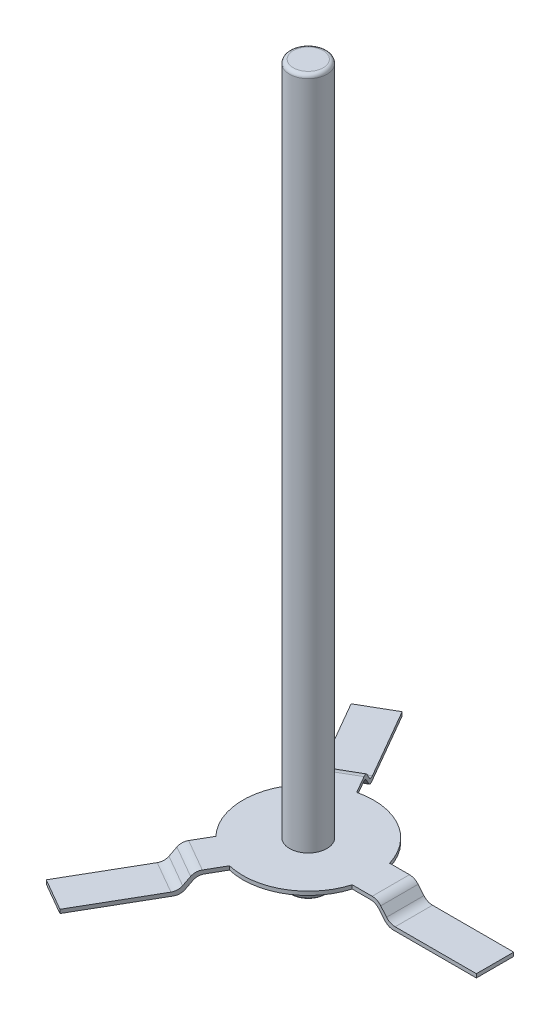
SolidWorks part; units mm, degrees
material "Ст. 3кп ГОСТ 380-2005"
ref_plane "Спереди" through (0, 0, 0) normal (0, 0, 1) x (1, 0, 0)
ref_plane "Сверху" through (0, 0, 0) normal (0, 1, 0) x (1, 0, 0)
ref_plane "Справа" through (0, 0, 0) normal (1, 0, 0) x (0, 0, -1)
sketch "Эскиз1" plane through (0, 0, 0) normal (0, 1, 0) x (1, 0, 0)
  circle A0 centre (0, 0) radius 0.5
  dimension "D1" = 1
extrude "Бобышка-Вытянуть1" add sketch "Эскиз1" along normal blind 19.15
ref_plane "Плоскость1" through (0, 1, 0) normal (0, 1, 0) x (1, 0, 0)
sketch "Эскиз2" plane through (0, 1, 0) normal (0, 1, 0) x (1, 0, 0)
  circle A0 centre (0, 0) radius 1.75
  circle A1 centre (0, 0) radius 0.5
  circle A2 centre (0, 0) radius 0.5 construction
  dimension "D1" = 3.5
extrude "Бобышка-Вытянуть2" add sketch "Эскиз2" along normal blind 0.1
sketch "Эскиз3" plane through (0, 0, 0) normal (0, 0, 1) x (1, 0, 0)
  line L0 (1.5, 1) -> (2.3034, 1)
  line L1 (2.3034, 1) -> (2.639, 0.6)
  line L2 (2.639, 0.6) -> (5, 0.6)
  line L3 (5, 0.6) -> (5, 0.7)
  line L4 (5, 0.7) -> (2.6856, 0.7)
  line L5 (2.6856, 0.7) -> (2.35, 1.1)
  line L6 (2.35, 1.1) -> (1.5, 1.1)
  line L7 (1.75, 1.1) -> (-1.75, 1.1) construction
  line L8 (-1.75, 1) -> (1.75, 1) construction
  line L9 (1.5, 1.1) -> (1.5, 1)
  line L10 (-0.5, 0) -> (0.5, 0) construction
  dimension "D1" = 5
  dimension "D2" = 2.35
  dimension "D3" = 0.1
  dimension "D4" = 130
  dimension "D5" = 1.5
  dimension "D6" = 0.6
extrude "Бобышка-Вытянуть3" add sketch "Эскиз3" along normal mid plane 1
pattern_circular "Круговой массив1" count 3 over 360 about axis through (0, 0, 0) along (0, 1, 0) of "Бобышка-Вытянуть3"
fillet "Скругление2" radius 0.3 12 edges at (-1.175, 1.1, -2.0352) (-1.3428, 0.7, -2.3258) (-1.3195, 0.6, -2.2854) (-1.1517, 1, -1.9948) (2.639, 0.6, 0) (2.3034, 1, 0) (2.6856, 0.7, 0) (2.35, 1.1, 0) (-1.3195, 0.6, 2.2854) (-1.1517, 1, 1.9948) (-1.3428, 0.7, 2.3258) (-1.175, 1.1, 2.0352)
fillet "Скругление3" radius 0.1 2 edges at (0, 19.15, 0.5) (0, 0, 0.5)
